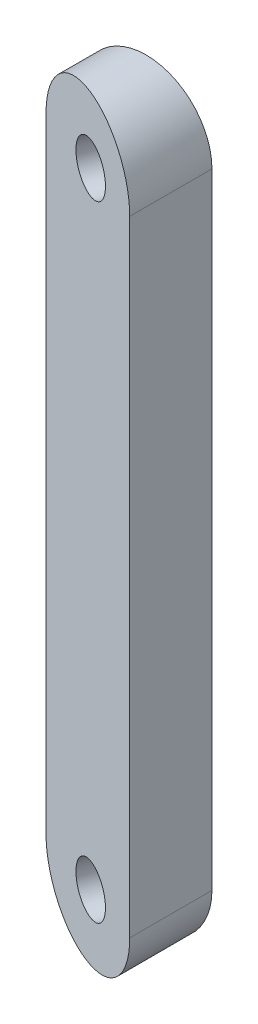
SolidWorks part; units mm, degrees
ref_plane "Front Plane" through (0, 0, 0) normal (0, 0, 1) x (1, 0, 0)
ref_plane "Top Plane" through (0, 0, 0) normal (0, 1, 0) x (1, 0, 0)
ref_plane "Right Plane" through (0, 0, 0) normal (1, 0, 0) x (0, 0, -1)
sketch "Sketch1" plane through (0, 0, 0) normal (0, 0, 1) x (1, 0, 0)
  line L0 (68.3946, 19) -> (68.3946, -19) construction
  line L1 (72.3946, 19) -> (72.3946, -19)
  line L2 (64.3946, 19) -> (64.3946, -19)
  line L3 (68.3946, 0) -> (0, 0) construction
  arc A0 (72.3946, 19) -> (64.3946, 19) centre (68.3946, 19) ccw
  arc A1 (64.3946, -19) -> (72.3946, -19) centre (68.3946, -19) ccw
  ellipse E0 centre (69.9909, 19) end of major axis (71.5871, 19) minor radius 1.5 (69.9909, 20.5) -> (69.9909, 17.5) ccw construction
  point P2 (68.3946, 0)
  dimension "D1" = 38
  dimension "D2" = 8
extrude "Boss-Extrude1" add sketch "Sketch1" along normal blind 5
sketch "Sketch2" plane through (0, 0, 0) normal (0, 1, 0) x (1, 0, 0)
  line L0 (72.3946, -5) -> (64.3946, -2.0882)
  line L1 (64.3946, -5) -> (64.3946, 0) construction
  line L2 (64.3946, -2.0882) -> (64.3946, -5)
  line L3 (64.3946, -5) -> (72.3946, -5)
  line L4 (44.9462, 18.6968) -> (85.353, 3.9899) construction
extrude "Cut-Extrude1" cut sketch "Sketch2" against normal through all both and the other way through all
sketch "Sketch3" plane through (6.8616, 0, -18.8521) normal (-0.342, 0, 0.9397) x (0.9397, 0, 0.342)
  circle A0 centre (65.7699, 19) radius 1.5 construction
  circle A1 centre (65.7699, -19) radius 1.5 construction
  circle A2 centre (65.7699, 19) radius 1.5
  circle A3 centre (65.7699, -19) radius 1.5
extrude "Cut-Extrude2" cut sketch "Sketch3" against normal blind 91
